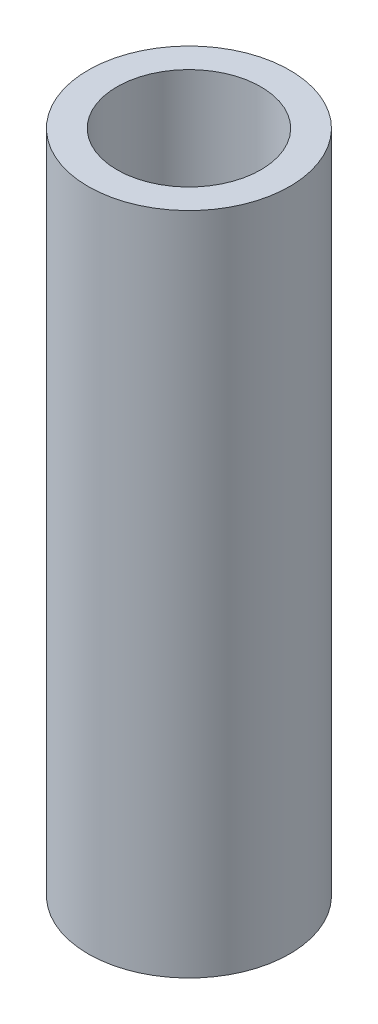
SolidWorks part; units mm, degrees
ref_plane "Front Plane" through (0, 0, 0) normal (0, 0, 1) x (1, 0, 0)
ref_plane "Top Plane" through (0, 0, 0) normal (0, 1, 0) x (1, 0, 0)
ref_plane "Right Plane" through (0, 0, 0) normal (1, 0, 0) x (0, 0, -1)
sketch "Sketch1" plane through (0, 0, 0) normal (0, 1, 0) x (1, 0, 0)
  circle A0 centre (0, 0) radius 4.572
  circle A1 centre (0, 0) radius 3.2639
  dimension "D1" = 6.5278
  dimension "D2" = 9.144
extrude "Boss-Extrude1" add sketch "Sketch1" along normal blind 30.1498
